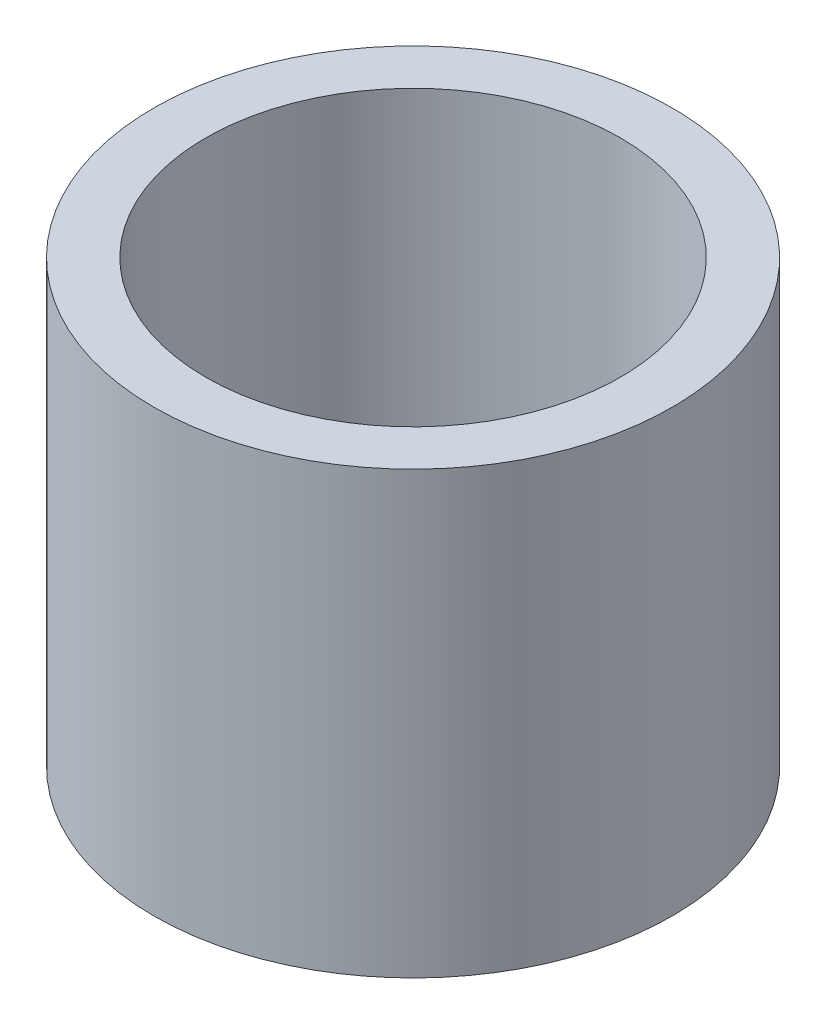
SolidWorks part; units mm, degrees
ref_plane "Front Plane" through (0, 0, 0) normal (0, 0, 1) x (1, 0, 0)
ref_plane "Top Plane" through (0, 0, 0) normal (0, 1, 0) x (1, 0, 0)
ref_plane "Right Plane" through (0, 0, 0) normal (1, 0, 0) x (0, 0, -1)
sketch "Sketch1" plane through (0, 0, 0) normal (0, 1, 0) x (1, 0, 0)
  circle A0 centre (0, 0) radius 20
  circle A1 centre (0, 0) radius 16
  dimension "D1" = 40
  dimension "D2" = 32
extrude "Boss-Extrude1" add sketch "Sketch1" along normal mid plane 34
